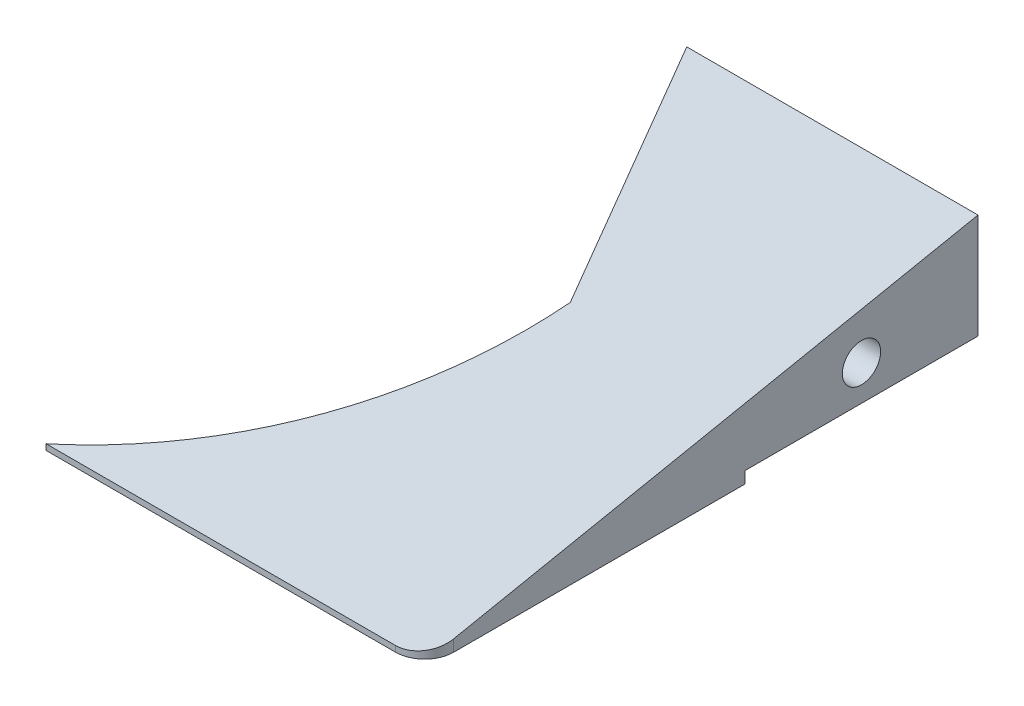
SolidWorks part; units mm, degrees
material "AISI 1020"
ref_plane "Plano frontal" through (0, 0, 0) normal (0, 0, 1) x (1, 0, 0)
ref_plane "Plano superior" through (0, 0, 0) normal (0, 1, 0) x (1, 0, 0)
ref_plane "Plano direito" through (0, 0, 0) normal (1, 0, 0) x (0, 0, -1)
sketch "Esboço1" plane through (0, 0, 0) normal (0, 0, 1) x (1, 0, 0)
  line L1 (-65, 10) -> (65, 10)
  line L2 (-65, 10) -> (-65, -10)
  line L3 (-65, -10) -> (65, -10)
  line L4 (65, 10) -> (65, -10)
  line L5 (-65, 10) -> (65, -10) construction
  line L6 (-65, -10) -> (65, 10) construction
  point P0 (0, 0)
  dimension "D1" = 130
  dimension "D2" = 20
extrude "Ressalto-extrusão1" add sketch "Esboço1" along normal blind 95
sketch "Esboço2" plane through (0, 10, 0) normal (0, 1, 0) x (1, 0, 0)
  line L0 (15, 0) -> (-65, 0)
  line L2 (65, -95) -> (65, 0) construction
  line L3 (35, -40) -> (15, 0)
  line L4 (-65, -95) -> (-65, 0) construction
  line L6 (-65, -95) -> (-65, 0)
  line L7 (65, -95) -> (-65, -95) construction
  line L8 (65, 0) -> (-65, 0) construction
  line L9 (0, -95) -> (-65, -95)
  arc A0 (0, -95) -> (35, -40) centre (-38.0495, -32.1503) ccw
  dimension "D3" = 65
  dimension "D5" = 73.47
  dimension "D1" = 50
  dimension "D2" = 30
  dimension "D4" = 40
extrude "Corte-extrusão2" cut sketch "Esboço2" against normal up to next contours A0 L3 L0 L6 L9
sketch "Esboço3" plane through (65, 0, 0) normal (1, 0, 0) x (0, 0, -1)
  line L0 (0, 10) -> (-95, -9)
  line L1 (-95, -10) -> (-95, 10) construction
  dimension "D1" = 1
extrude "Corte-extrusão3" cut sketch "Esboço3" against normal through all and the other way through all flip side to cut
hole_wizard "Broca de rosquear de cano para tarraxa de 1/82" positions "Esboço7" profile "Esboço8" hole size "1/8" standard "Ansi Inch"
sketch "Esboço7" plane through (65, 0, 0) normal (1, 0, 0) x (0, 0, -1)
  line L0 (0, -10) -> (0, 10) construction
  line L1 (-95, -10) -> (0, -10) construction
  point P0 (-20, -1.945)
  dimension "D1" = 20
  dimension "D2" = 8.055
sketch "Esboço8" plane through (65, -1.945, 20) normal (0, 1, 0) x (0, 0, -1)
  line L0 (0, 0) -> (0, 11.9768)
  line L1 (0, 11.9768) -> (3.29, 10)
  line L2 (3.29, 10) -> (3.29, 0)
  line L5 (3.29, 0) -> (0, 0)
  line L10 (0, 11.9768) -> (-3.29, 10) construction
  line L11 (0, -6.35) -> (0, 107.95) construction
  dimension "Hole Dia." = 6.58
  dimension "Hole Depth" = 10
  dimension "Drill Angle" = 118
hole_wizard "Broca de rosquear de cano para tarraxa de 1/83" positions "Esboço10" profile "Esboço11" hole size "1/8" standard "Ansi Inch"
sketch "Esboço10" plane through (12, 0, -6) normal (-0.8944, 0, 0.4472) x (0.4472, 0, 0.8944)
  line L0 (6.7082, -10) -> (6.7082, 10) construction
  line L1 (6.7082, -10) -> (51.4296, -10) construction
  point P0 (26.7082, -1.945)
  dimension "D1" = 20
  dimension "D2" = 8.055
sketch "Esboço11" plane through (23.9443, -1.945, 17.8885) normal (0, 1, 0) x (0.4472, 0, 0.8944)
  line L0 (0, 0) -> (0, 11.9768)
  line L1 (0, 11.9768) -> (3.29, 10)
  line L2 (3.29, 10) -> (3.29, 0)
  line L5 (3.29, 0) -> (0, 0)
  line L10 (0, 11.9768) -> (-3.29, 10) construction
  line L11 (0, -6.35) -> (0, 107.95) construction
  dimension "Hole Dia." = 6.58
  dimension "Hole Depth" = 10
  dimension "Drill Angle" = 118
fillet "Filete2" radius 5 1 edges at (65, -9.5, 95)
sketch "Esboço16" plane through (0, 0, 0) normal (0, 0, -1) x (-1, 0, 0)
  line L0 (-65, -10) -> (-15, -10)
  line L1 (-15, -10) -> (-15, -8)
  line L2 (-15, -10) -> (-15, 10) construction
  line L3 (-15, -8) -> (-65, -8)
  line L4 (-65, -8) -> (-65, -10)
  dimension "D1" = 2
extrude "Corte-extrusão6" cut sketch "Esboço16" against normal blind 40
